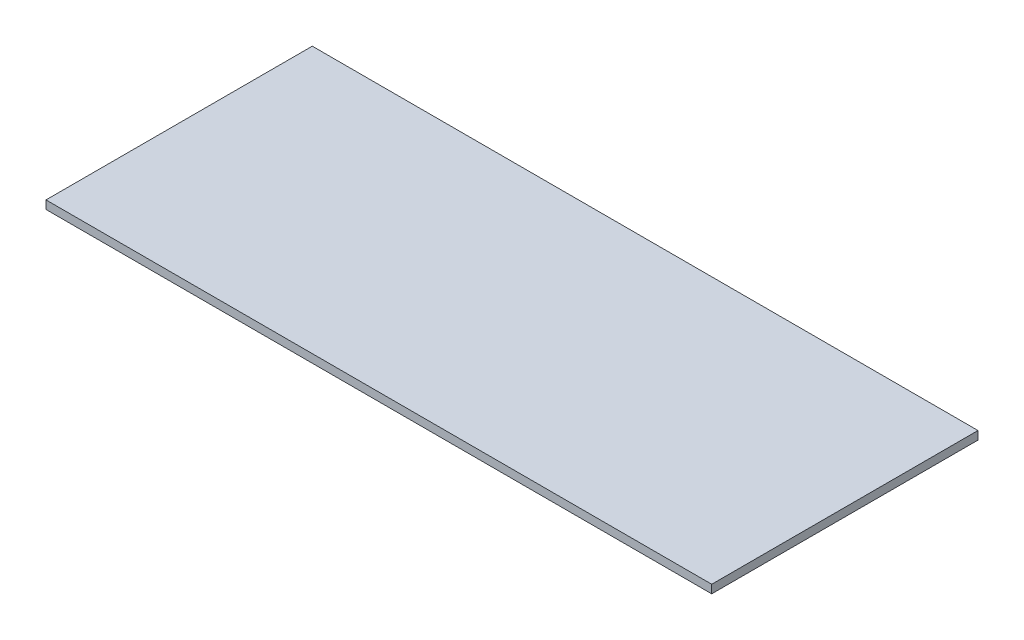
SolidWorks part; units mm, degrees
ref_plane "Alzado" through (0, 0, 0) normal (0, 0, 1) x (1, 0, 0)
ref_plane "Planta" through (0, 0, 0) normal (0, 1, 0) x (1, 0, 0)
ref_plane "Vista lateral" through (0, 0, 0) normal (1, 0, 0) x (0, 0, -1)
sketch "Croquis1" plane through (0, 0, 0) normal (0, 1, 0) x (1, 0, 0)
  line L1 (-254, 101.6) -> (254, 101.6)
  line L2 (-254, 101.6) -> (-254, -101.6)
  line L3 (-254, -101.6) -> (254, -101.6)
  line L4 (254, 101.6) -> (254, -101.6)
  line L5 (-254, 101.6) -> (254, -101.6) construction
  line L6 (-254, -101.6) -> (254, 101.6) construction
  point P0 (0, 0)
  dimension "D1" = 508
  dimension "D2" = 203.2
extrude "Saliente-Extruir1" add sketch "Croquis1" along normal blind 6.35
